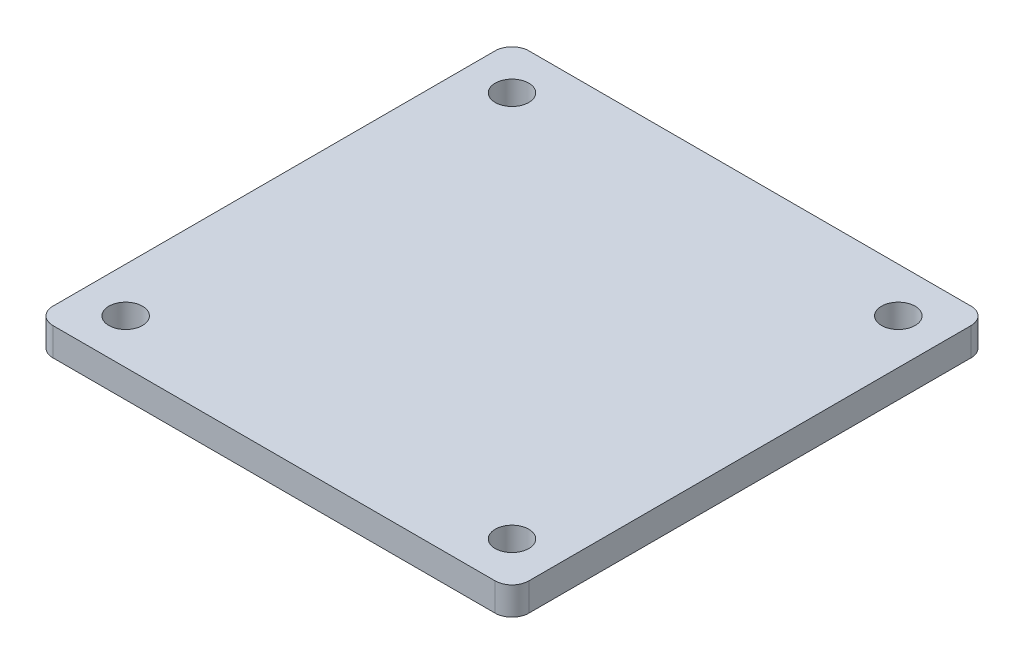
SolidWorks part; units mm, degrees
ref_plane "Front Plane" through (0, 0, 0) normal (0, 0, 1) x (1, 0, 0)
ref_plane "Top Plane" through (0, 0, 0) normal (0, 1, 0) x (1, 0, 0)
ref_plane "Right Plane" through (0, 0, 0) normal (1, 0, 0) x (0, 0, -1)
sketch "Sketch1" plane through (0, 0, 0) normal (0, 1, 0) x (1, 0, 0)
  line L1 (-42.5, -42.5) -> (42.5, -42.5)
  line L2 (-42.5, -42.5) -> (-42.5, 42.5)
  line L3 (-42.5, 42.5) -> (42.5, 42.5)
  line L4 (42.5, -42.5) -> (42.5, 42.5)
  point P0 (0, 0)
  dimension "D1" = 85
  dimension "D2" = 85
extrude "Boss-Extrude1" add sketch "Sketch1" along normal blind 5
fillet "Fillet1" radius 3 4 edges at (-42.5, 2.5, -42.5) (-42.5, 2.5, 42.5) (42.5, 2.5, -42.5) (42.5, 2.5, 42.5)
sketch "Sketch2" plane through (0, 5, 0) normal (0, 1, 0) x (1, 0, 0)
  line L0 (39.5, 42.5) -> (-39.5, 42.5) construction
  line L1 (-42.5, 39.5) -> (-42.5, -39.5) construction
  line L2 (0, 56.3454) -> (0, -63.34) construction
  line L3 (0, -2.75) -> (0, 2.75) construction
  line L4 (-67.459, 0) -> (69.3243, 0) construction
  line L5 (-2.75, 0) -> (2.75, 0) construction
  circle A0 centre (-34.5, 34.5) radius 3
  circle A4 centre (-34.5, -34.5) radius 3
  circle A5 centre (34.5, -34.5) radius 3
  circle A6 centre (34.5, 34.5) radius 3
  dimension "D3" = 6
  dimension "D1" = 8
  dimension "D2" = 8
extrude "Cut-Extrude1" cut sketch "Sketch2" against normal through all
sketch "Sketch4" plane through (0, 0, 0) normal (0, 0, 1) x (1, 0, 0)
  line L0 (-30.4845, 5) -> (-37.3991, 30.8056)
  line L1 (-39.5, 5) -> (39.5, 5) construction
  line L2 (-30.4845, -5.5316) -> (-30.4845, 39.2677) construction
  dimension "D1" = 75
